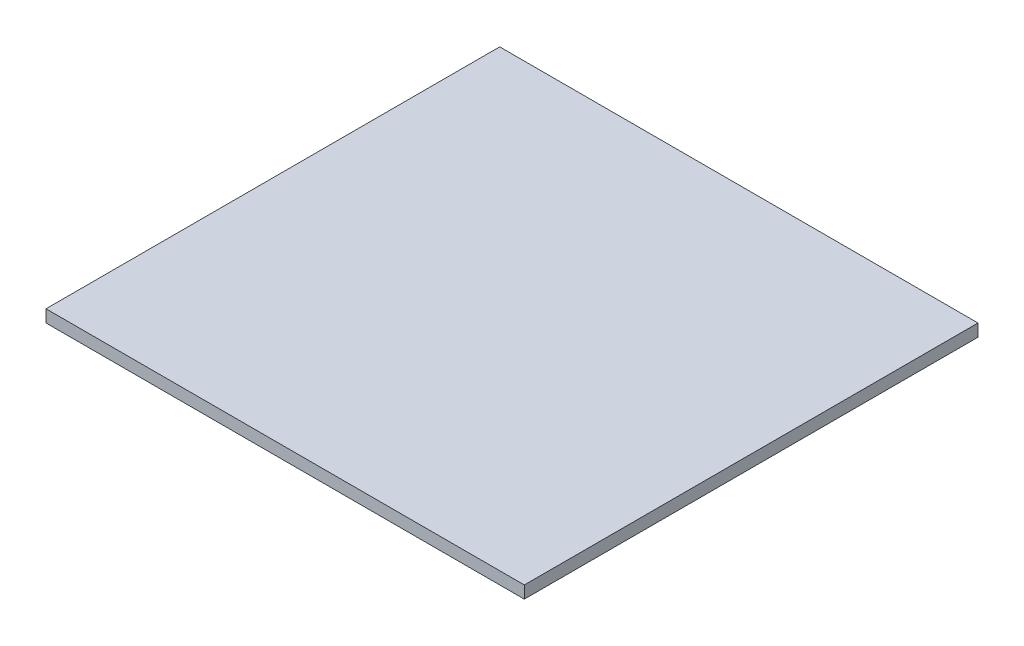
SolidWorks part; units mm, degrees
ref_plane "Alzado" through (0, 0, 0) normal (0, 0, 1) x (1, 0, 0)
ref_plane "Planta" through (0, 0, 0) normal (0, 1, 0) x (1, 0, 0)
ref_plane "Vista lateral" through (0, 0, 0) normal (1, 0, 0) x (0, 0, -1)
sketch "Croquis1" plane through (0, 0, 0) normal (0, 1, 0) x (1, 0, 0)
  line L1 (-36.9, 35) -> (36.9, 35)
  line L2 (-36.9, 35) -> (-36.9, -35)
  line L3 (-36.9, -35) -> (36.9, -35)
  line L4 (36.9, 35) -> (36.9, -35)
  line L5 (-36.9, 35) -> (36.9, -35) construction
  line L6 (-36.9, -35) -> (36.9, 35) construction
  point P0 (0, 0)
  dimension "D1" = 73.8
  dimension "D2" = 70
extrude "Saliente-Extruir1" add sketch "Croquis1" along normal blind 1.9
